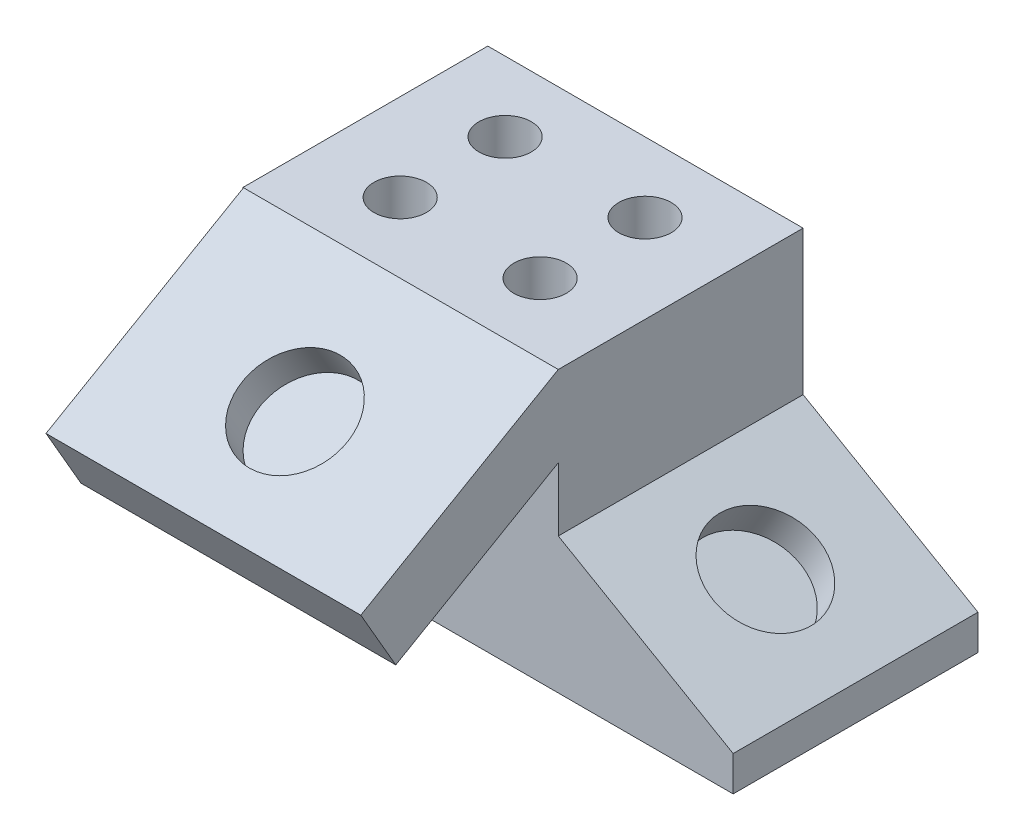
SolidWorks part; units mm, degrees
ref_plane "Front Plane" through (0, 0, 0) normal (0, 0, 1) x (1, 0, 0)
ref_plane "Top Plane" through (0, 0, 0) normal (0, 1, 0) x (1, 0, 0)
ref_plane "Right Plane" through (0, 0, 0) normal (1, 0, 0) x (0, 0, -1)
sketch "Sketch1" plane through (0, 0, 0) normal (0, 0, 1) x (1, 0, 0)
  line L0 (0, 0) -> (0, 50.8625)
  line L1 (0, 50.8625) -> (57.2489, 50.8625)
  line L2 (57.2489, 50.8625) -> (57.2489, 24.6809)
  line L3 (57.2489, 24.6809) -> (88.9989, 6.35)
  line L4 (88.9989, 6.35) -> (88.9989, 0)
  line L5 (88.9989, 0) -> (0, 0)
  dimension "D1" = 60
  dimension "D2" = 6.35
  dimension "D3" = 57.2489
  dimension "D4" = 50.8625
  dimension "D5" = 31.75
extrude "Boss-Extrude1" add sketch "Sketch1" along normal blind 44.45
sketch "Sketch2" plane through (57.2489, 0, 0) normal (1, 0, 0) x (0, 0, -1)
  line L0 (-44.45, 50.8625) -> (-80.3052, 30.1615)
  line L1 (-80.3052, 30.1615) -> (-73.9552, 19.163)
  line L2 (-73.9552, 19.163) -> (-44.45, 36.1978)
  line L3 (-44.45, 24.6809) -> (-44.45, 50.8625) construction
  line L4 (-44.45, 50.8625) -> (0, 50.8625) construction
  line L5 (-44.45, 50.8625) -> (-44.45, 36.1978)
  dimension "D1" = 12.7
  dimension "D2" = 30
  dimension "D3" = 41.402
extrude "Boss-Extrude2" add sketch "Sketch2" against normal blind 57.15
sketch "Sketch5" plane through (0, 57.3943, 33.1366) normal (0, 0.866, 0.5) x (1, 0, 0)
  line L0 (57.2489, -13.0636) -> (0.0989, -13.0636) construction
  line L1 (0.0989, -13.0636) -> (0.0989, -54.4656) construction
  circle A0 centre (28.8009, -35.4156) radius 9.525
  dimension "D1" = 19.05
  dimension "D2" = 22.352
  dimension "D3" = 28.702
extrude "Cut-Extrude1" cut sketch "Sketch5" against normal blind 6.35 contours A0
sketch "Sketch6" plane through (24.9994, 43.3002, 0) normal (0.5, 0.866, 0) x (0.866, -0.5, 0)
  line L0 (73.9003, -44.45) -> (37.2386, -44.45) construction
  line L1 (73.9003, -44.45) -> (73.9003, 0) construction
  circle A0 centre (54.8503, -22.098) radius 9.525
  point P6 (76.5632, -68.7221)
  dimension "D1" = 19.05
  dimension "D2" = 22.352
  dimension "D3" = 19.05
extrude "Cut-Extrude2" cut sketch "Sketch6" against normal blind 6.35 contours A0
sketch "Sketch7" plane through (0, 50.8625, 0) normal (0, 1, 0) x (1, 0, 0)
  line L0 (57.2489, -44.45) -> (0.0989, -44.45) construction
  line L1 (57.2489, -44.45) -> (57.2489, 0) construction
  circle A0 centre (15.8469, -12.7) radius 4.7625
  circle A1 centre (15.8469, -31.75) radius 4.7625
  circle A2 centre (41.2469, -31.75) radius 4.7625
  circle A3 centre (41.2469, -12.7) radius 4.7625
  point P8 (0, 0)
  point P9 (0, 0)
  point P10 (0, 0)
  point P13 (0, 0)
  dimension "D1" = 9.525
  dimension "D5" = 16.002
  dimension "D2" = 12.7
  dimension "D3" = 19.05
  dimension "D4" = 25.4
extrude "Cut-Extrude3" cut sketch "Sketch7" against normal blind 12.7
